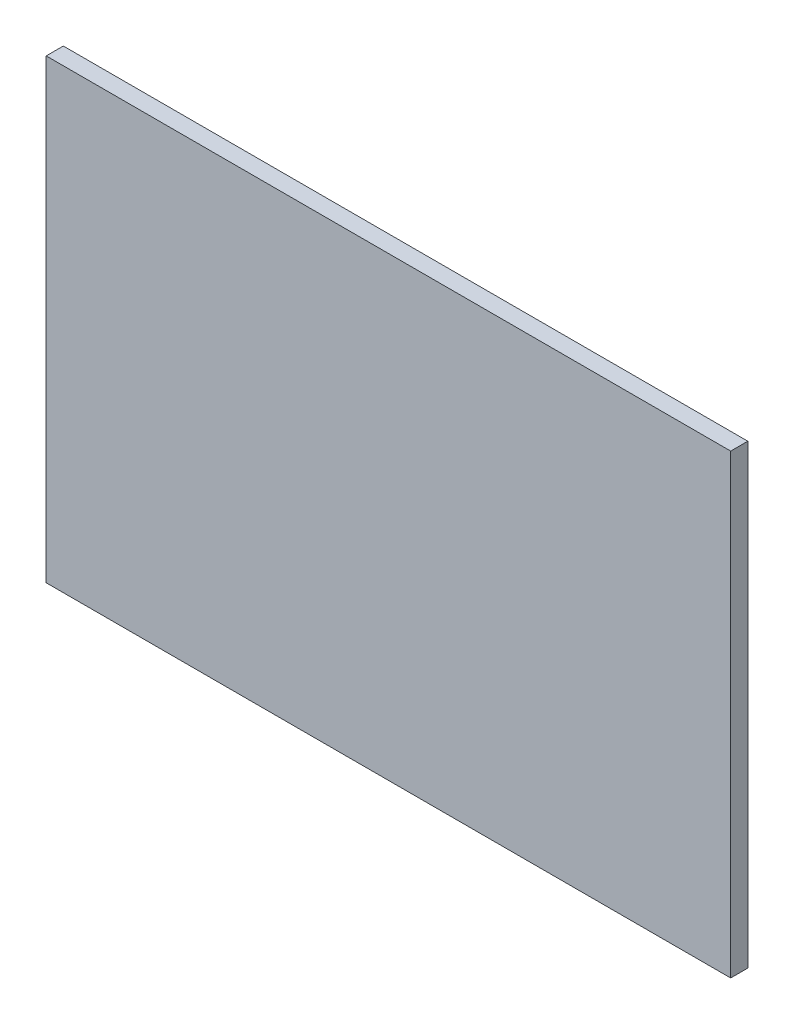
SolidWorks part; units mm, degrees
ref_plane "Alzado" through (0, 0, 0) normal (0, 0, 1) x (1, 0, 0)
ref_plane "Planta" through (0, 0, 0) normal (0, 1, 0) x (1, 0, 0)
ref_plane "Vista lateral" through (0, 0, 0) normal (1, 0, 0) x (0, 0, -1)
sketch "Croquis1" plane through (0, 0, 0) normal (0, 0, 1) x (1, 0, 0)
  line L0 (-300, 200) -> (300, -200) construction
  line L1 (-300, 200) -> (300, 200)
  line L2 (-300, 200) -> (-300, -200)
  line L3 (-300, -200) -> (300, -200)
  line L4 (300, 200) -> (300, -200)
  line L5 (-300, -200) -> (300, 200) construction
  dimension "D1" = 400
  dimension "D2" = 600
extrude "Saliente-Extruir1" add sketch "Croquis1" along normal blind 15
